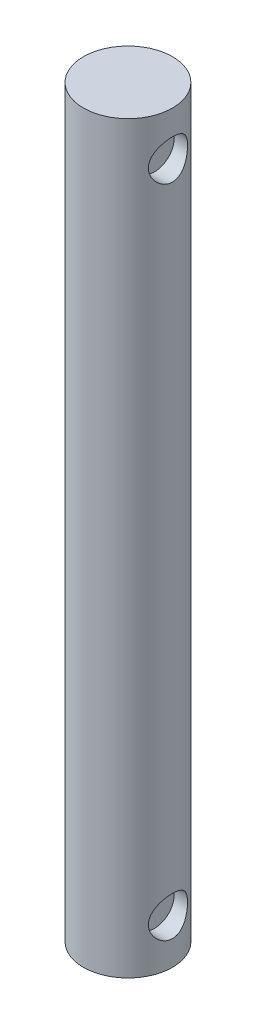
SolidWorks part; units mm, degrees
ref_plane "前视基准面" through (0, 0, 0) normal (0, 0, 1) x (1, 0, 0)
ref_plane "上视基准面" through (0, 0, 0) normal (0, 1, 0) x (1, 0, 0)
ref_plane "右视基准面" through (0, 0, 0) normal (1, 0, 0) x (0, 0, -1)
other "Configuration Table"
sketch "草图1" plane through (0, 0, 0) normal (0, 1, 0) x (1, 0, 0)
  circle A0 centre (0, 0) radius 2.5
extrude "凸台-拉伸1" add sketch "草图1" along normal blind 41.8
sketch "草图5" plane through (0, 41.8, 0) normal (0, 1, 0) x (1, 0, 0)
  line L0 (0, 0) -> (2.5, 0) construction
  line L1 (2.5, 0) -> (2.5, -3.1952) construction
  circle A0 centre (0, 0) radius 2.5 construction
ref_plane "基准面2" through (2.5, 0, 0) normal (1, 0, 0) x (0, 0, -1)
sketch "草图6" plane through (2.5, 0, 0) normal (1, 0, 0) x (0, 0, -1)
  line L0 (0, 41.8) -> (0, 39.3) construction
  line L1 (0, 41.8) -> (-3.1952, 41.8) construction
  line L2 (0, 0) -> (0, 2.5) construction
  circle A0 centre (0, 39.3) radius 1.1
  circle A1 centre (0, 2.5) radius 1.1
extrude "切除-拉伸1" cut sketch "草图6" against normal blind 1
